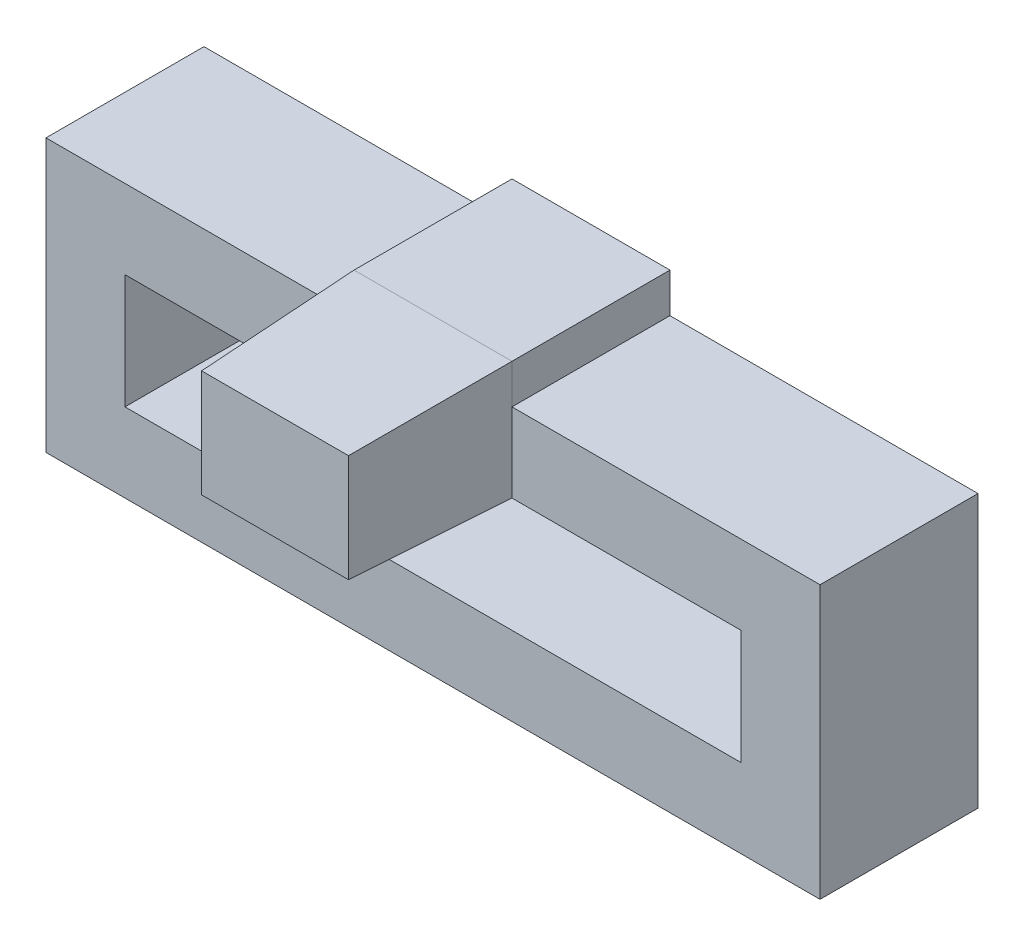
SolidWorks part; units mm, degrees
ref_plane "Front" through (0, 0, 0) normal (0, 0, 1) x (1, 0, 0)
ref_plane "Top" through (0, 0, 0) normal (0, 1, 0) x (1, 0, 0)
ref_plane "Right" through (0, 0, 0) normal (1, 0, 0) x (0, 0, -1)
sketch "Esquisse1" plane through (0, 0, 0) normal (0, 0, 1) x (1, 0, 0)
  line L1 (0, 0) -> (15.6, 0)
  line L2 (0, 0) -> (0, 2.9)
  line L3 (0, 2.9) -> (15.6, 2.9)
  line L4 (15.6, 0) -> (15.6, 2.9)
  dimension "D1" = 2.9
  dimension "D2" = 15.6
extrude "Extru.-Mince1" add sketch "Esquisse1" along normal blind 4 thin
sketch "Esquisse2" plane through (0, 0, 0) normal (0, 0, 1) x (1, 0, 0)
  line L1 (5.8, 2.9) -> (9.8, 2.9)
  line L2 (5.8, 2.9) -> (5.8, 5.9)
  line L3 (5.8, 5.9) -> (9.8, 5.9)
  line L4 (9.8, 2.9) -> (9.8, 5.9)
  line L5 (7.8, 17.3638) -> (7.8, -7.8315) construction
  line L6 (17.6, -2) -> (17.6, 4.9) construction
  line L7 (-2, 4.9) -> (-2, -2) construction
  line L8 (15.6, 2.9) -> (0, 2.9) construction
  dimension "D1" = 4
  dimension "D2" = 3
extrude "Boss.-Extru.2" add sketch "Esquisse2" along normal blind 4
ref_plane "Plan1" through (0, 0, 4) normal (0, 0, 1) x (1, 0, 0)
sketch "Esquisse3" plane through (0, 0, 4) normal (0, 0, 1) x (1, 0, 0)
  line L0 (15.6, 2.9) -> (0, 2.9) construction
  line L1 (5.8, 5.9) -> (9.8, 5.9)
  line L2 (5.8, 5.9) -> (5.8, 2.9)
  line L3 (5.8, 2.9) -> (9.8, 2.9)
  line L4 (9.8, 5.9) -> (9.8, 2.9)
extrude "Boss.-Extru.3" add sketch "Esquisse3" along normal blind 4 draft 2 contours L2 L1 L4 L3
